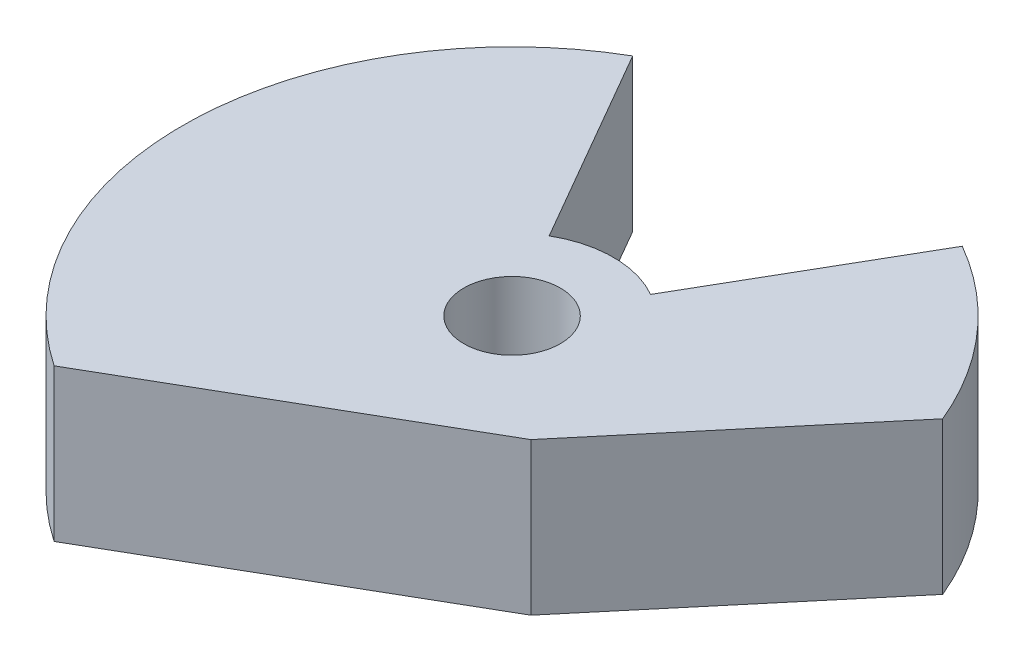
SolidWorks part; units mm, degrees
material "ABS"
ref_plane "Front Plane" through (0, 0, 0) normal (0, 0, 1) x (1, 0, 0)
ref_plane "Top Plane" through (0, 0, 0) normal (0, 1, 0) x (1, 0, 0)
ref_plane "Right Plane" through (0, 0, 0) normal (1, 0, 0) x (0, 0, -1)
sketch "Sketch1" plane through (0, 0, 0) normal (0, 1, 0) x (1, 0, 0)
  line L0 (-16.25, 28.1458) -> (-5, 8.6603)
  line L1 (5, 8.6603) -> (16.25, 28.1458)
  line L2 (0, 0) -> (0, 20) construction
  line L3 (0, 0) -> (-5, 8.6603) construction
  line L4 (5, 8.6603) -> (0, 0) construction
  arc A0 (-16.25, 28.1458) -> (16.25, 28.1458) centre (0, 0) ccw
  circle A1 centre (0, 0) radius 4.7625
  arc A2 (5, 8.6603) -> (-5, 8.6603) centre (0, 0) ccw
  dimension "D1" = 9.525
  dimension "D2" = 65
  dimension "D3" = 20
  dimension "D4" = 30
  dimension "D5" = 30
extrude "Boss-Extrude1" add sketch "Sketch1" along normal blind 15
sketch "Sketch2" plane through (0, 15, 0) normal (0, 1, 0) x (1, 0, 0)
  line L0 (4.0536, 2.5) -> (4.0536, -2.5)
  arc A0 (4.0536, -2.5) -> (4.0536, 2.5) centre (0, 0) ccw
  circle A1 centre (0, 0) radius 4.7625 construction
  dimension "D1" = 5
extrude "Shaft D" [suppressed] add sketch "Sketch2" against normal up to surface (10 mm away)
sketch "Sketch3" plane through (0, 15, 0) normal (0, 1, 0) x (1, 0, 0)
  line L0 (-16.25, 28.1458) -> (-13.25, 29.8779)
  line L1 (-13.25, 29.8779) -> (-13.25, 22.9497)
  line L2 (-5, 8.6603) -> (-16.25, 28.1458) construction
  line L3 (-13.25, 22.9497) -> (-16.25, 28.1458)
  line L4 (0, 0) -> (0, 30.6174) construction
  line L5 (13.25, 22.9497) -> (16.25, 28.1458)
  line L6 (13.25, 29.8779) -> (13.25, 22.9497)
  line L7 (16.25, 28.1458) -> (13.25, 29.8779)
  dimension "D1" = 6
extrude "Boss-Extrude2" [suppressed] add sketch "Sketch3" against normal up to surface (15 mm away)
sketch "Sketch4" plane through (0, 15, 0) normal (0, 1, 0) x (1, 0, 0)
  line L0 (-148.943, 0) -> (142.5774, 0) construction
  line L1 (0, 0) -> (-107.5774, -62.1099) construction
  line L2 (0, 0) -> (49.4281, -41.4751) construction
  line L8 (0, 0) -> (41.4751, 49.4281) construction
  line L9 (0, 0) -> (62.1099, -107.5774) construction
  line L10 (-107.5774, -62.1099) -> (62.1099, -107.5774) construction
  line L11 (41.4751, 49.4281) -> (49.4281, -41.4751) construction
  line L14 (11.4907, -9.6418) -> (45.5038, 30.8934)
  line L15 (11.4907, -9.6418) -> (-38.9929, -38.7885)
  arc A2 (-38.9929, -38.7885) -> (45.5038, 30.8934) centre (0, 0) ccw
  dimension "D4" = 55
  dimension "D1" = 40
  dimension "D3" = 30
  dimension "D5" = 15
extrude "Cut-Extrude1" cut sketch "Sketch4" against normal through all
